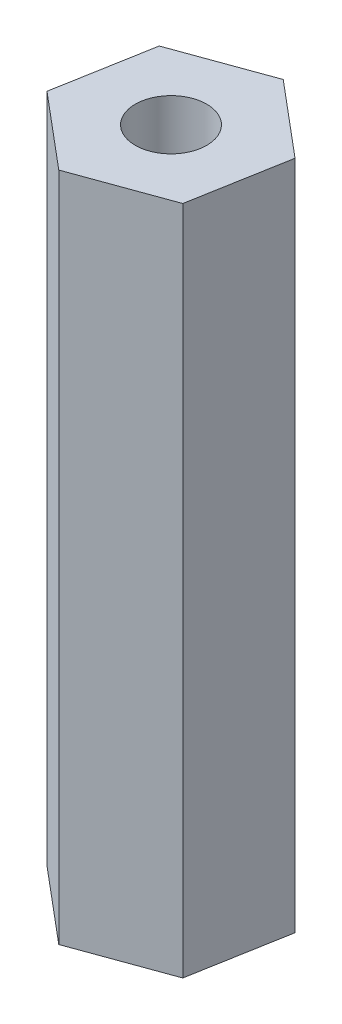
SolidWorks part; units mm, degrees
ref_plane "Front" through (0, 0, 0) normal (0, 0, 1) x (1, 0, 0)
ref_plane "Top" through (0, 0, 0) normal (0, 1, 0) x (1, 0, 0)
ref_plane "Right" through (0, 0, 0) normal (1, 0, 0) x (0, 0, -1)
sketch "Sketch1" plane through (0, 0, 0) normal (0, 1, 0) x (1, 0, 0)
  line L1 (-2.806, 2.3595) -> (-3.4464, -1.2502)
  line L2 (-3.4464, -1.2502) -> (-0.6405, -3.6098)
  line L3 (-0.6405, -3.6098) -> (2.806, -2.3595)
  line L4 (2.806, -2.3595) -> (3.4464, 1.2502)
  line L5 (3.4464, 1.2502) -> (0.6405, 3.6098)
  line L6 (0.6405, 3.6098) -> (-2.806, 2.3595)
  circle A0 centre (0, 0) radius 3.175 construction
  dimension "D1" = 6.35
extrude "Boss-Extrude1" add sketch "Sketch1" along normal blind 25.4
sketch "Sketch2" plane through (0, 25.4, 0) normal (0, 1, 0) x (1, 0, 0)
  circle A0 centre (0, 0) radius 1.3525
  dimension "D1" = 2.7051
extrude "Cut-Extrude1" cut sketch "Sketch2" against normal through all
